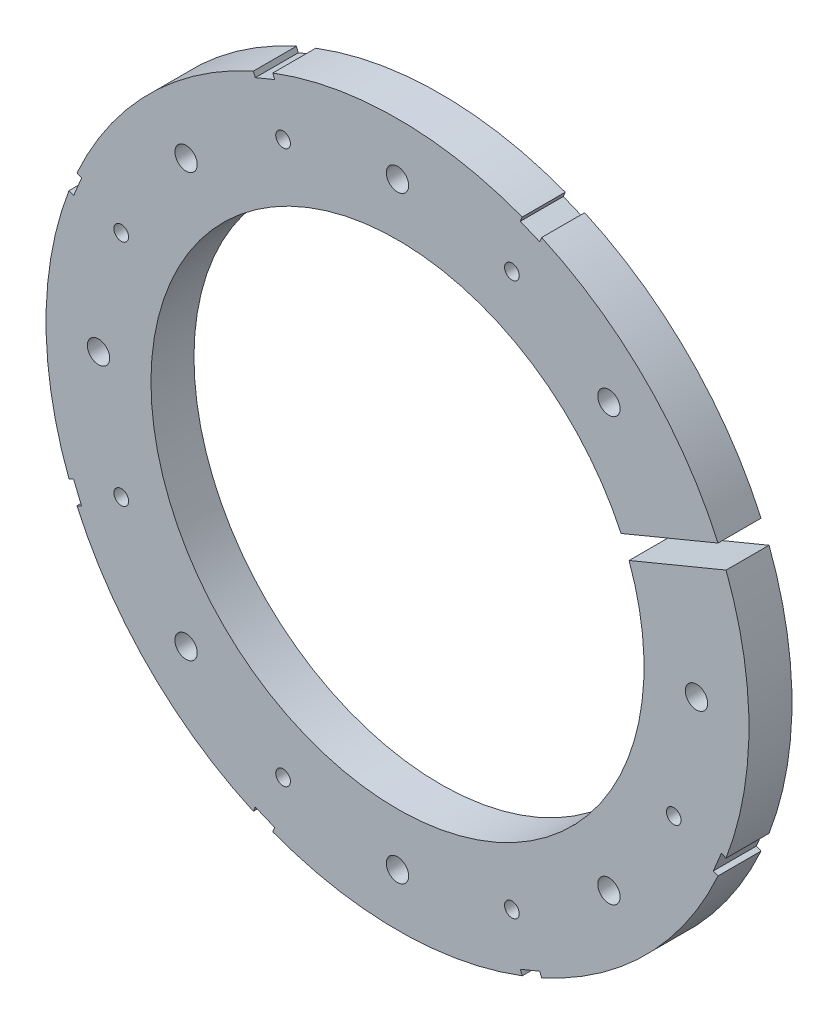
SolidWorks part; units mm, degrees
material "Brass"
ref_plane "Front Plane" through (0, 0, 0) normal (0, 0, 1) x (1, 0, 0)
ref_plane "Top Plane" through (0, 0, 0) normal (0, 1, 0) x (1, 0, 0)
ref_plane "Right Plane" through (0, 0, 0) normal (1, 0, 0) x (0, 0, -1)
sketch "Sketch4" plane through (0, 0, 0) normal (0, 0, 1) x (1, 0, 0)
  circle A0 centre (0, 0) radius 42.545
  dimension "D1" = 85.09
extrude "Boss-Extrude2" add sketch "Sketch4" along normal blind 5.207
sketch "Sketch5" plane through (0, 0, 5.207) normal (0, 0, 1) x (1, 0, 0)
  circle A0 centre (0, 0) radius 29.845
  circle A1 centre (0, 0) radius 42.545 construction
  dimension "D1" = 12.7
extrude "Cut-Extrude5" cut sketch "Sketch5" against normal through all
sketch "Sketch8" plane through (0, 0, 5.207) normal (0, 0, 1) x (1, 0, 0)
  line L0 (45.2737, 20.1276) -> (26.5005, 12.3515)
  line L1 (45.2737, 20.1276) -> (46.2458, 17.781)
  line L2 (26.5005, 12.3515) -> (27.4725, 10.0049)
  line L3 (46.2458, 17.781) -> (27.4725, 10.0049)
  line L4 (45.2737, 20.1276) -> (27.4725, 10.0049) construction
  line L5 (26.5005, 12.3515) -> (46.2458, 17.781) construction
  line L6 (0, 0) -> (50.4438, 0) construction
  line L7 (17.6976, 39.4071) -> (15.3509, 40.3791)
  line L8 (17.6976, 39.4071) -> (17.2116, 38.2338)
  line L9 (15.3509, 40.3791) -> (14.8649, 39.2058)
  line L10 (17.2116, 38.2338) -> (14.8649, 39.2058)
  line L11 (15.3509, 40.3791) -> (17.2116, 38.2338) construction
  line L12 (17.6976, 39.4071) -> (14.8649, 39.2058) construction
  line L13 (-15.3509, 40.3791) -> (-17.6976, 39.4071)
  line L14 (-15.3509, 40.3791) -> (-14.8649, 39.2058)
  line L15 (-14.8649, 39.2058) -> (-17.2116, 38.2338)
  line L16 (-17.6976, 39.4071) -> (-17.2116, 38.2338)
  line L17 (-15.3509, 40.3791) -> (-17.2116, 38.2338) construction
  line L18 (-17.6976, 39.4071) -> (-14.8649, 39.2058) construction
  line L19 (-39.4071, 17.6976) -> (-40.3791, 15.3509)
  line L20 (-39.4071, 17.6976) -> (-38.2338, 17.2116)
  line L21 (-38.2338, 17.2116) -> (-39.2058, 14.8649)
  line L22 (-40.3791, 15.3509) -> (-39.2058, 14.8649)
  line L23 (-39.4071, 17.6976) -> (-39.2058, 14.8649) construction
  line L24 (-40.3791, 15.3509) -> (-38.2338, 17.2116) construction
  line L25 (-40.3791, -15.3509) -> (-39.4071, -17.6976)
  line L26 (-40.3791, -15.3509) -> (-39.2058, -14.8649)
  line L27 (-39.2058, -14.8649) -> (-38.2338, -17.2116)
  line L28 (-39.4071, -17.6976) -> (-38.2338, -17.2116)
  line L29 (-40.3791, -15.3509) -> (-38.2338, -17.2116) construction
  line L30 (-39.4071, -17.6976) -> (-39.2058, -14.8649) construction
  line L31 (-17.6976, -39.4071) -> (-15.3509, -40.3791)
  line L32 (-17.6976, -39.4071) -> (-17.2116, -38.2338)
  line L33 (-17.2116, -38.2338) -> (-14.8649, -39.2058)
  line L34 (-15.3509, -40.3791) -> (-14.8649, -39.2058)
  line L35 (-17.6976, -39.4071) -> (-14.8649, -39.2058) construction
  line L36 (-15.3509, -40.3791) -> (-17.2116, -38.2338) construction
  line L37 (15.3509, -40.3791) -> (17.6976, -39.4071)
  line L38 (15.3509, -40.3791) -> (14.8649, -39.2058)
  line L39 (14.8649, -39.2058) -> (17.2116, -38.2338)
  line L40 (17.6976, -39.4071) -> (17.2116, -38.2338)
  line L41 (15.3509, -40.3791) -> (17.2116, -38.2338) construction
  line L42 (17.6976, -39.4071) -> (14.8649, -39.2058) construction
  line L43 (39.4071, -17.6976) -> (40.3791, -15.3509)
  line L44 (39.4071, -17.6976) -> (38.2338, -17.2116)
  line L45 (38.2338, -17.2116) -> (39.2058, -14.8649)
  line L46 (40.3791, -15.3509) -> (39.2058, -14.8649)
  line L47 (39.4071, -17.6976) -> (39.2058, -14.8649) construction
  line L48 (40.3791, -15.3509) -> (38.2338, -17.2116) construction
  circle A0 centre (0, 0) radius 29.845 construction
  circle A1 centre (0, 0) radius 42.545 construction
  point P1 (36.3731, 15.0662)
  point P3 (16.2813, 39.3065)
  point P11 (-16.2813, 39.3065)
  point P20 (-39.3065, 16.2813)
  point P25 (-39.3065, -16.2813)
  point P26 (0, 0)
  point P31 (-16.2813, -39.3065)
  point P36 (16.2813, -39.3065)
  point P41 (39.3065, -16.2813)
  point P46 (0, 0)
  dimension "D1" = 20.32
  dimension "D2" = 9.525
  dimension "D3" = 2.54
  dimension "D4" = 22.5
  dimension "D5" = 1.27
  dimension "D6" = 2.54
  dimension "D7" = 1.27
  dimension "D8" = 1.27
  dimension "D9" = 0.635
  dimension "D10" = 67.5
  dimension "D12" = 0.635
  dimension "D13" = 22.5
  dimension "D11" = 7
extrude "Cut-Extrude11" cut sketch "Sketch8" against normal through all
hole_wizard "#6-32 Tapped Hole1" positions "Sketch10" profile "Sketch9" tap size "#6-32" standard "ANSI Inch" end condition through all
sketch "Sketch10" plane through (0, 0, 5.207) normal (0, 0, 1) x (1, 0, 0)
  line L0 (0, 0) -> (36.195, 0) construction
  line L3 (0, 0) -> (25.5937, 25.5937) construction
  line L5 (0, 0) -> (25.5937, -25.5937) construction
  arc A0 (27.0622, 12.5842) -> (28.0342, 10.2375) centre (0, 0) ccw construction
  point P0 (36.195, 0)
  point P10 (25.5937, -25.5937)
  point P11 (0, -36.195)
  point P12 (-25.5937, -25.5937)
  point P13 (-36.195, 0)
  point P14 (-25.5937, 25.5937)
  point P15 (0, 36.195)
  point P16 (25.5937, 25.5937)
  dimension "D1" = 6.35
  dimension "D3" = 45
  dimension "D4" = 45
  dimension "D5" = 6.35
  dimension "D2" = 8
cosmetic thread "Hole Thread1" parameters "D2"=3.5052
cosmetic thread "Hole Thread2" parameters "D2"=3.5052
cosmetic thread "Hole Thread3" parameters "D2"=3.5052
cosmetic thread "Hole Thread4" parameters "D2"=3.5052
cosmetic thread "Hole Thread5" parameters "D2"=3.5052
cosmetic thread "Hole Thread6" parameters "D2"=3.5052
cosmetic thread "Hole Thread7" parameters "D2"=3.5052
cosmetic thread "Hole Thread8" parameters "D2"=3.5052
sketch "Sketch9" plane through (36.195, 0, 5.207) normal (1, 0, 0) x (0, -1, 0)
  line L0 (0, 0) -> (0, 5.207)
  line L1 (0, 5.207) -> (1.3525, 5.207)
  line L2 (1.3525, 5.207) -> (1.3525, 0)
  line L5 (1.3525, 0) -> (0, 0)
  line L11 (0, -6.35) -> (0, 107.95) construction
  dimension "Thru Tap Drill Dia." = 2.7051
  dimension "Thru Tap Drill Depth" = 5.207
hole_wizard "#2-56 Tapped Hole1" positions "Sketch12" profile "Sketch11" tap size "#2-56" standard "ANSI Inch"
sketch "Sketch12" plane through (0, 0, 5.207) normal (0, 0, 1) x (1, 0, 0)
  line L0 (0, 0) -> (13.8512, 33.4398) construction
  line L2 (0, 0) -> (36.195, 0) construction
  line L4 (0, 0) -> (13.8512, 33.4398) construction
  line L5 (0, 0) -> (-13.8512, 33.4398) construction
  arc A0 (27.0622, 12.5842) -> (28.0342, 10.2375) centre (0, 0) ccw construction
  point P0 (13.8512, 33.4398)
  point P27 (-13.8512, 33.4398)
  point P28 (-33.4398, 13.8512)
  point P29 (-33.4398, -13.8512)
  point P30 (-13.8512, -33.4398)
  point P31 (13.8512, -33.4398)
  point P32 (33.4398, -13.8512)
  point P44 (33.4398, 13.8512) [skipped]
  dimension "D1" = 6.35
  dimension "D2" = 67.5
  dimension "D4" = 315
  dimension "D5" = 36.195
  dimension "D6" = 6.35
  dimension "D3" = 8
sketch "Sketch11" plane through (13.8512, 33.4398, 5.207) normal (1, 0, 0) x (0, -1, 0)
  line L0 (0, 0) -> (0, 3.8362)
  line L1 (0, 3.8362) -> (0.889, 3.302)
  line L2 (0.889, 3.302) -> (0.889, 0)
  line L5 (0.889, 0) -> (0, 0)
  line L10 (0, 3.8362) -> (-0.889, 3.302) construction
  line L11 (0, -6.35) -> (0, 107.95) construction
  dimension "Tap Drill Dia." = 1.778
  dimension "Tap Drill Depth" = 3.302
  dimension "Drill Angle" = 118
cosmetic thread "Hole Thread9" parameters "D1"=3.302, "D2"=2.1844
cosmetic thread "Hole Thread10" parameters "D1"=3.302, "D2"=2.1844
cosmetic thread "Hole Thread11" parameters "D1"=3.302, "D2"=2.1844
cosmetic thread "Hole Thread12" parameters "D1"=3.302, "D2"=2.1844
cosmetic thread "Hole Thread13" parameters "D1"=3.302, "D2"=2.1844
cosmetic thread "Hole Thread14" parameters "D1"=3.302, "D2"=2.1844
cosmetic thread "Hole Thread15" parameters "D1"=3.302, "D2"=2.1844
